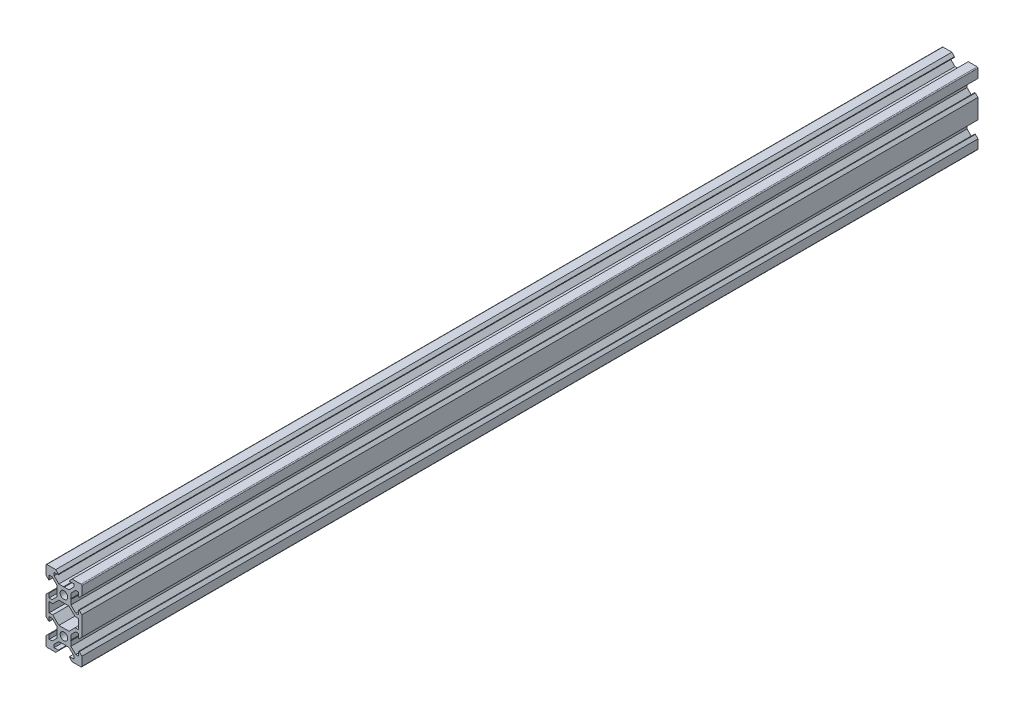
SolidWorks part; units mm, degrees
material "6061-T6 (SS)"
ref_plane "Front Plane" through (0, 0, 0) normal (0, 0, 1) x (1, 0, 0)
ref_plane "Top Plane" through (0, 0, 0) normal (0, 1, 0) x (1, 0, 0)
ref_plane "Right Plane" through (0, 0, 0) normal (1, 0, 0) x (0, 0, -1)
sketch "Sketch1" plane through (0, 0, 0) normal (0, 0, 1) x (1, 0, 0)
  line L0 (0, 0) -> (10, 0) construction
  line L1 (9.5, -20) -> (-9.5, -20)
  line L2 (10, -19.5) -> (10, 19.5)
  line L3 (9.5, 20) -> (-9.5, 20)
  line L4 (-10, -19.5) -> (-10, 19.5)
  line L5 (10, -20) -> (-10, 20) construction
  line L6 (10, 20) -> (-10, -20) construction
  circle A0 centre (0, 10) radius 2.1
  circle A1 centre (0, -10) radius 2.1
  arc A2 (-9.5, -20) -> (-10, -19.5) centre (-9.5, -19.5) cw
  arc A3 (9.5, -20) -> (10, -19.5) centre (9.5, -19.5) ccw
  arc A4 (10, 19.5) -> (9.5, 20) centre (9.5, 19.5) ccw
  arc A5 (-9.5, 20) -> (-10, 19.5) centre (-9.5, 19.5) ccw
  point P0 (0, 0)
  line B0 (0, 10) -> (0, 20) construction
  line B1 (0, 13.69) -> (-0.21, 13.9)
  line B2 (-0.21, 13.9) -> (-2.8393, 13.9)
  line B3 (-2.8393, 13.9) -> (-5.5, 16.5607)
  line B4 (-5.5, 16.5607) -> (-5.5, 18.2)
  line B5 (-5.5, 18.2) -> (-3.125, 18.2)
  line B6 (-3.125, 18.2) -> (-3.125, 18.545)
  line B7 (-3.125, 18.545) -> (-4.58, 20)
  line B8 (-4.58, 20) -> (4.58, 20)
  line B9 (0, 10) -> (-5.9132, 15.9132) construction
  line B10 (3.125, 18.545) -> (4.58, 20)
  line B11 (3.125, 18.2) -> (3.125, 18.545)
  line B12 (5.5, 18.2) -> (3.125, 18.2)
  line B13 (5.5, 16.5607) -> (5.5, 18.2)
  line B14 (2.8393, 13.9) -> (5.5, 16.5607)
  line B15 (0.21, 13.9) -> (2.8393, 13.9)
  line B16 (0, 13.69) -> (0.21, 13.9)
  line B17 (0, 10) -> (-10, 10) construction
  line B18 (-3.69, 10) -> (-3.9, 9.79)
  line B19 (-3.9, 9.79) -> (-3.9, 7.1607)
  line B20 (-3.9, 7.1607) -> (-6.5607, 4.5)
  line B21 (-6.5607, 4.5) -> (-8.2, 4.5)
  line B22 (-8.2, 4.5) -> (-8.2, 6.875)
  line B23 (-8.2, 6.875) -> (-8.545, 6.875)
  line B24 (-8.545, 6.875) -> (-10, 5.42)
  line B25 (-10, 5.42) -> (-10, 14.58)
  line B26 (0, 10) -> (-5.9132, 4.0868) construction
  line B27 (-8.545, 13.125) -> (-10, 14.58)
  line B28 (-8.2, 13.125) -> (-8.545, 13.125)
  line B29 (-8.2, 15.5) -> (-8.2, 13.125)
  line B30 (-6.5607, 15.5) -> (-8.2, 15.5)
  line B31 (-3.9, 12.8393) -> (-6.5607, 15.5)
  line B32 (-3.9, 10.21) -> (-3.9, 12.8393)
  line B33 (-3.69, 10) -> (-3.9, 10.21)
  line B34 (0, -10) -> (-10, -10) construction
  line B35 (-3.69, -10) -> (-3.9, -10.21)
  line B36 (-3.9, -10.21) -> (-3.9, -12.8393)
  line B37 (-3.9, -12.8393) -> (-6.5607, -15.5)
  line B38 (-6.5607, -15.5) -> (-8.2, -15.5)
  line B39 (-8.2, -15.5) -> (-8.2, -13.125)
  line B40 (-8.2, -13.125) -> (-8.545, -13.125)
  line B41 (-8.545, -13.125) -> (-10, -14.58)
  line B42 (-10, -14.58) -> (-10, -5.42)
  line B43 (0, -10) -> (-5.9132, -15.9132) construction
  line B44 (-8.545, -6.875) -> (-10, -5.42)
  line B45 (-8.2, -6.875) -> (-8.545, -6.875)
  line B46 (-8.2, -4.5) -> (-8.2, -6.875)
  line B47 (-6.5607, -4.5) -> (-8.2, -4.5)
  line B48 (-3.9, -7.1607) -> (-6.5607, -4.5)
  line B49 (-3.9, -9.79) -> (-3.9, -7.1607)
  line B50 (-3.69, -10) -> (-3.9, -9.79)
  line B51 (0, -10) -> (0, -20) construction
  line B52 (0, -13.69) -> (0.21, -13.9)
  line B53 (0.21, -13.9) -> (2.8393, -13.9)
  line B54 (2.8393, -13.9) -> (5.5, -16.5607)
  line B55 (5.5, -16.5607) -> (5.5, -18.2)
  line B56 (5.5, -18.2) -> (3.125, -18.2)
  line B57 (3.125, -18.2) -> (3.125, -18.545)
  line B58 (3.125, -18.545) -> (4.58, -20)
  line B59 (4.58, -20) -> (-4.58, -20)
  line B60 (0, -10) -> (5.9132, -15.9132) construction
  line B61 (-3.125, -18.545) -> (-4.58, -20)
  line B62 (-3.125, -18.2) -> (-3.125, -18.545)
  line B63 (-5.5, -18.2) -> (-3.125, -18.2)
  line B64 (-5.5, -16.5607) -> (-5.5, -18.2)
  line B65 (-2.8393, -13.9) -> (-5.5, -16.5607)
  line B66 (-0.21, -13.9) -> (-2.8393, -13.9)
  line B67 (0, -13.69) -> (-0.21, -13.9)
  line B68 (0, -10) -> (10, -10) construction
  line B69 (3.69, -10) -> (3.9, -9.79)
  line B70 (3.9, -9.79) -> (3.9, -7.1607)
  line B71 (3.9, -7.1607) -> (6.5607, -4.5)
  line B72 (6.5607, -4.5) -> (8.2, -4.5)
  line B73 (8.2, -4.5) -> (8.2, -6.875)
  line B74 (8.2, -6.875) -> (8.545, -6.875)
  line B75 (8.545, -6.875) -> (10, -5.42)
  line B76 (10, -5.42) -> (10, -14.58)
  line B77 (0, -10) -> (5.9132, -4.0868) construction
  line B78 (8.545, -13.125) -> (10, -14.58)
  line B79 (8.2, -13.125) -> (8.545, -13.125)
  line B80 (8.2, -15.5) -> (8.2, -13.125)
  line B81 (6.5607, -15.5) -> (8.2, -15.5)
  line B82 (3.9, -12.8393) -> (6.5607, -15.5)
  line B83 (3.9, -10.21) -> (3.9, -12.8393)
  line B84 (3.69, -10) -> (3.9, -10.21)
  line B85 (0, 10) -> (10, 10) construction
  line B86 (3.69, 10) -> (3.9, 10.21)
  line B87 (3.9, 10.21) -> (3.9, 12.8393)
  line B88 (3.9, 12.8393) -> (6.5607, 15.5)
  line B89 (6.5607, 15.5) -> (8.2, 15.5)
  line B90 (8.2, 15.5) -> (8.2, 13.125)
  line B91 (8.2, 13.125) -> (8.545, 13.125)
  line B92 (8.545, 13.125) -> (10, 14.58)
  line B93 (10, 14.58) -> (10, 5.42)
  line B94 (0, 10) -> (5.9132, 15.9132) construction
  line B95 (8.545, 6.875) -> (10, 5.42)
  line B96 (8.2, 6.875) -> (8.545, 6.875)
  line B97 (8.2, 4.5) -> (8.2, 6.875)
  line B98 (6.5607, 4.5) -> (8.2, 4.5)
  line B99 (3.9, 7.1607) -> (6.5607, 4.5)
  line B100 (3.9, 9.79) -> (3.9, 7.1607)
  line B101 (3.69, 10) -> (3.9, 9.79)
  line B102 (-8.2, -2.7) -> (-8.2, 2.7)
  line B103 (-8.2, 2.7) -> (-6.2393, 2.7)
  line B104 (-6.2393, 2.7) -> (-2.8393, 6.1)
  line B105 (-2.8393, 6.1) -> (2.8393, 6.1)
  line B106 (0, 6.1) -> (0, 0) construction
  line B107 (0, 0) -> (-8.2, 0) construction
  line B108 (6.2393, 2.7) -> (2.8393, 6.1)
  line B109 (8.2, 2.7) -> (6.2393, 2.7)
  line B110 (8.2, -2.7) -> (8.2, 2.7)
  line B111 (8.2, -2.7) -> (6.2393, -2.7)
  line B112 (6.2393, -2.7) -> (2.8393, -6.1)
  line B113 (-2.8393, -6.1) -> (2.8393, -6.1)
  line B114 (-6.2393, -2.7) -> (-2.8393, -6.1)
  line B115 (-8.2, -2.7) -> (-6.2393, -2.7)
  line B116 (0, 6.1) -> (0, 10) construction
  line B117 (0, 10) -> (-5.0927, 4.9073) construction
  dimension "D4" = 4.2
  dimension "D5" = 0.5
  dimension "D1" = 20
  dimension "D2" = 40
  dimension "D3" = 20
sketch_block_instance "V Slot 1-4"
sketch_block "V Slot 1" parameters "D1"=10, "D2"=11, "D3"=4.3, "D4"=1.8, "D5"=0.21, "D6"=45, "D7"=9.16, "D8"=1.5, "D9"=6.25
sketch_block_instance "V Slot 1-5"
sketch_block_instance "V Slot 1-6"
sketch_block_instance "V Slot 1-7"
sketch_block_instance "V Slot 1-8"
sketch_block_instance "V Slot 1-9"
sketch_block_instance "Center Cutout 1-1"
sketch_block "Center Cutout 1" parameters "D1"=5.4, "D2"=12.2, "D3"=8.2, "D4"=45, "D5"=10, "D6"=1.5
extrude "Boss-Extrude1" add sketch "Sketch1" along normal blind 500 contours B101 B86 B87 B88 B89 B90 B91 B92 L2 A4 L3 B10 B11 B12 B13 B14 B15 B16 B1 B2 B3 B4 B5 B6 B7 A5 L4 B27 B28 B29 B30 B31 B32 B33 B18 B19 B20 B21 B22 B23 B24 B44 B45 B46 B47 B48 B49 B50 B35
